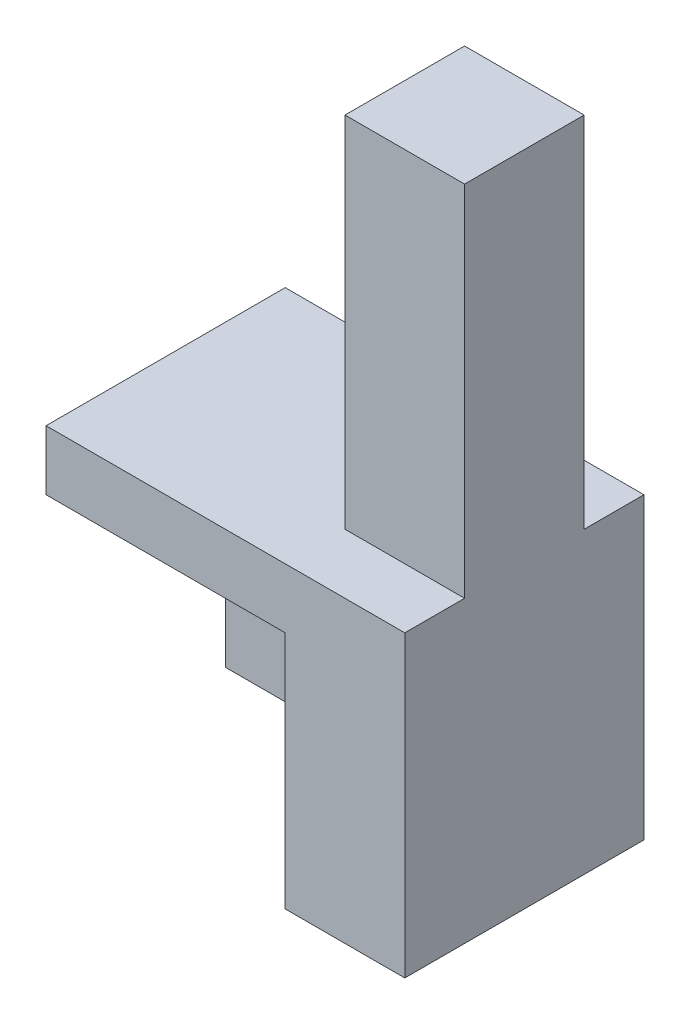
SolidWorks part; units mm, degrees
ref_plane "Front Plane" through (0, 0, 0) normal (0, 0, 1) x (1, 0, 0)
ref_plane "Top Plane" through (0, 0, 0) normal (0, 1, 0) x (1, 0, 0)
ref_plane "Right Plane" through (0, 0, 0) normal (1, 0, 0) x (0, 0, -1)
sketch "Sketch3" plane through (0, 0, 0) normal (0, 0, 1) x (1, 0, 0)
  line L0 (0, 0) -> (0, -5)
  line L1 (0, -5) -> (20, -5)
  line L2 (20, -5) -> (20, -25)
  line L3 (0, 0) -> (20, 0)
  line L4 (20, 0) -> (20, 30)
  line L5 (20, 30) -> (30, 30)
  line L6 (30, 30) -> (30, -25)
  line L7 (30, -25) -> (20, -25)
  dimension "D1" = 20
  dimension "D2" = 20
  dimension "D3" = 20
  dimension "D4" = 5
  dimension "D5" = 10
  dimension "D6" = 55
extrude "Boss-Extrude3" add sketch "Sketch3" along normal blind 10
sketch "Sketch4" plane through (0, 0, 0) normal (0, 0, -1) x (-1, 0, 0)
  line L5 (0, 0) -> (-30, 0)
  line L6 (0, 0) -> (0, -25)
  line L7 (0, -25) -> (-30, -25)
  line L8 (-30, 0) -> (-30, -25)
extrude "Boss-Extrude4" add sketch "Sketch4" along normal blind 5
sketch "Sketch5" plane through (0, 0, 10) normal (0, 0, 1) x (1, 0, 0)
  line L0 (0, 0) -> (0, -5)
  line L1 (0, -5) -> (20, -5)
  line L2 (20, -5) -> (20, -25)
  line L3 (20, -25) -> (30, -25)
  line L4 (30, -25) -> (30, 0)
  line L5 (30, 0) -> (0, 0)
extrude "Boss-Extrude5" add sketch "Sketch5" along normal blind 5
